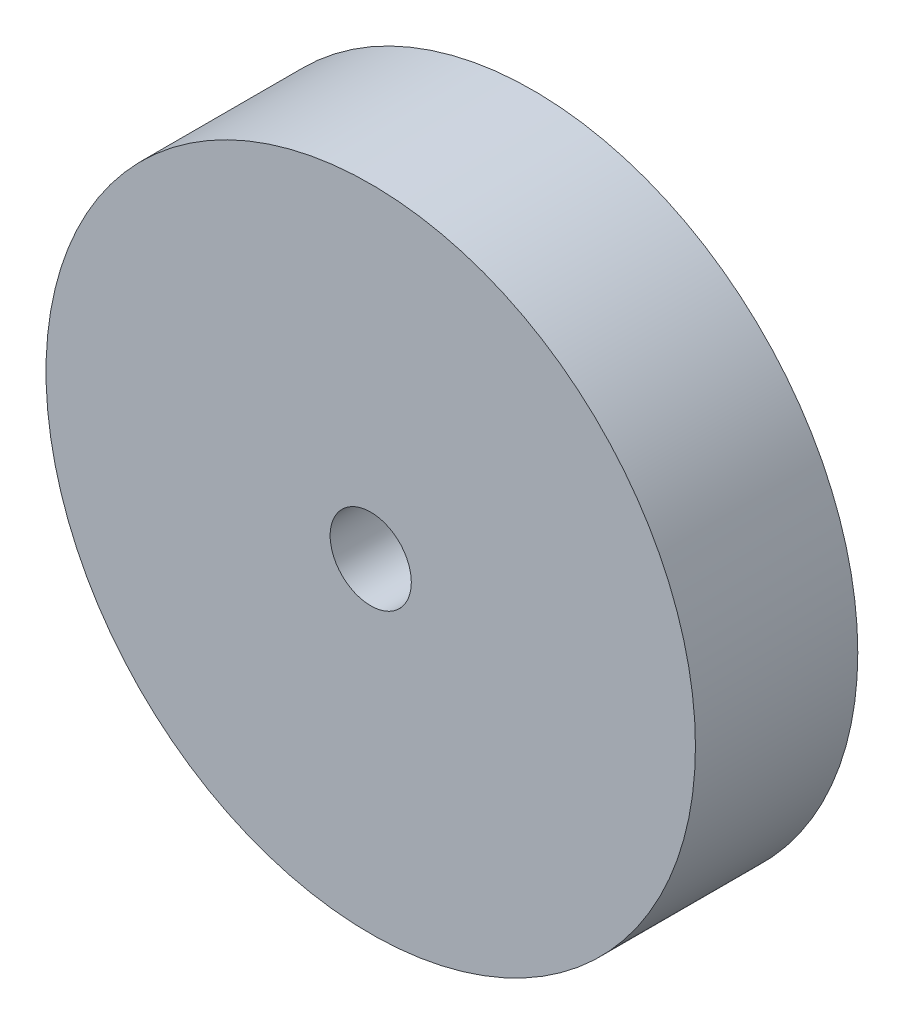
SolidWorks part; units mm, degrees
material "ASTM A36 Steel"
ref_plane "Front Plane" through (0, 0, 0) normal (0, 0, 1) x (1, 0, 0)
ref_plane "Top Plane" through (0, 0, 0) normal (0, 1, 0) x (1, 0, 0)
ref_plane "Right Plane" through (0, 0, 0) normal (1, 0, 0) x (0, 0, -1)
sketch "Sketch1" plane through (0, 0, 0) normal (0, 0, 1) x (1, 0, 0)
  circle A0 centre (0, 0) radius 25.4
  dimension "D1" = 50.8
extrude "Boss-Extrude1" add sketch "Sketch1" along normal blind 12.7
sketch "Sketch2" plane through (0, 0, 12.7) normal (0, 0, 1) x (1, 0, 0)
  circle A0 centre (0, 0) radius 3.175
  dimension "D1" = 6.35
extrude "Cut-Extrude1" cut sketch "Sketch2" against normal blind 6.35
